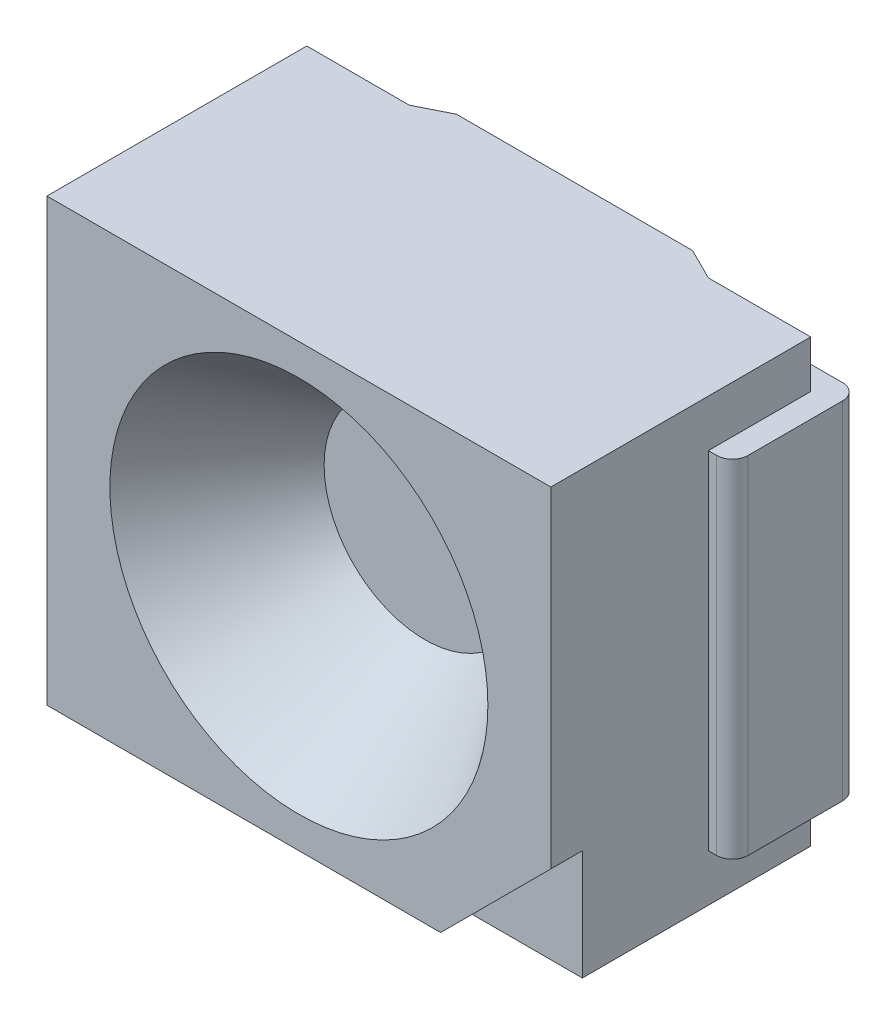
SolidWorks part; units mm, degrees
ref_plane "Front Plane" through (0, 0, 0) normal (0, 0, 1) x (1, 0, 0)
ref_plane "Top Plane" through (0, 0, 0) normal (0, 1, 0) x (1, 0, 0)
ref_plane "Right Plane" through (0, 0, 0) normal (1, 0, 0) x (0, 0, -1)
sketch "Sketch1" plane through (0, 0, 0) normal (0, 0, 1) x (1, 0, 0)
  line L1 (0, 0) -> (3.2, 0)
  line L2 (0, 0) -> (0, 2.8)
  line L3 (0, 2.8) -> (3.2, 2.8)
  line L4 (3.2, 0) -> (3.2, 2.8)
  dimension "D1" = 3.2
  dimension "D2" = 2.8
extrude "Boss-Extrude1" add sketch "Sketch1" along normal blind 1.75
sketch "Sketch2" plane through (0, 0, 1.75) normal (0, 0, 1) x (1, 0, 0)
  line L0 (3.2, 0) -> (3.2, 0.7)
  line L1 (3.2, 0) -> (3.2, 2.8) construction
  line L2 (3.2, 0.7) -> (2.5, 0)
  line L3 (0, 0) -> (3.2, 0) construction
  line L4 (2.5, 0) -> (3.2, 0)
  dimension "D1" = 0.7
  dimension "D2" = 0.7
extrude "Cut-Extrude1" cut sketch "Sketch2" against normal blind 0.2
sketch "Sketch3" plane through (0, 0, 1.75) normal (0, 0, 1) x (1, 0, 0)
  line L0 (3.2, 2.8) -> (0, 0) construction
  line L1 (0, 0) -> (0, 2.8) construction
  line L2 (0, 2.8) -> (3.2, 0) construction
  circle A0 centre (1.6, 1.4) radius 1.2
  dimension "D1" = 2.4
extrude "Cut-Extrude2" cut sketch "Sketch3" against normal blind 0.8 draft 35
sketch "Sketch5" plane through (0, 0, 0) normal (0, -1, 0) x (1, 0, 0)
  line L0 (1.6, 0) -> (1.6, 1.75) construction
  line L1 (0, 0) -> (3.2, 0) construction
  line L2 (0, 1.75) -> (2.5, 1.75) construction
  line L3 (0.85, 0) -> (2.35, 0) construction
  line L4 (0, 0.1) -> (0.65, 0.1)
  line L5 (0, 0.1) -> (0, 0)
  line L6 (0, 0) -> (0.65, 0)
  line L8 (2.55, 0.1) -> (3.2, 0.1)
  line L10 (2.55, 0) -> (3.2, 0)
  line L11 (3.2, 0.1) -> (3.2, 0)
  line L12 (0.65, 0.1) -> (0.85, 0)
  line L13 (0.85, 0) -> (0.65, 0)
  line L14 (2.55, 0.1) -> (2.35, 0)
  line L15 (2.35, 0) -> (2.55, 0)
  dimension "D1" = 0.1
  dimension "D2" = 0.65
  dimension "D3" = 1.5
  dimension "D4" = 0.1
  dimension "D5" = 0.65
extrude "Cut-Extrude3" cut sketch "Sketch5" against normal through all
sketch "Sketch6" plane through (0, 0, 0.1) normal (0, 0, -1) x (-1, 0, 0)
  line L0 (-2.875, 2.8) -> (-2.875, 0) construction
  line L1 (-3.2, 2.8) -> (-2.55, 2.8) construction
  line L2 (-3.2, 0) -> (-2.55, 0) construction
  line L3 (-2.875, 0) -> (-0.325, 0) construction
  line L4 (-0.65, 0) -> (0, 0) construction
  line L5 (-0.325, 0) -> (-0.325, 2.8) construction
  line L6 (-0.65, 2.8) -> (0, 2.8) construction
  line L7 (-3.2, 1.4) -> (0, 1.4) construction
  line L8 (-3.3525, 2.5) -> (-2.5525, 2.5)
  line L9 (-3.3525, 2.5) -> (-3.3525, 0.3)
  line L10 (-3.3525, 0.3) -> (-2.5525, 0.3)
  line L11 (-2.5525, 2.5) -> (-2.5525, 0.3)
  line L12 (-3.2, 2.8) -> (-3.2, 0) construction
  line L13 (0, 2.8) -> (0, 0) construction
  line L14 (0.15, 2.5) -> (0.15, 0.3)
  line L15 (-0.65, 2.5) -> (0.15, 2.5)
  line L16 (-0.65, 0.3) -> (0.15, 0.3)
  line L17 (-0.65, 2.5) -> (-0.65, 0.3)
  line L18 (-0.1725, 2.8) -> (-0.1725, 0) construction
  dimension "D1" = 0.8
  dimension "D2" = 2.2
  dimension "D3" = 0.8
  dimension "D4" = 2.2
extrude "Boss-Extrude3" add sketch "Sketch6" along normal blind 0.15
sketch "Sketch7" plane through (0, 0, 0.1) normal (0, 0, 1) x (1, 0, 0)
  line L0 (0, 0.3) -> (-0.15, 0.3) construction
  line L1 (-0.15, 2.5) -> (0, 2.5)
  line L2 (-0.15, 2.5) -> (-0.15, 0.3)
  line L3 (-0.15, 0.3) -> (0, 0.3)
  line L4 (0, 2.5) -> (0, 0.3)
  line L5 (0, 2.8) -> (0, 0) construction
  line L7 (3.3525, 0.3) -> (3.2, 0.3)
  line L8 (3.3525, 0.3) -> (3.3525, 2.5)
  line L9 (3.3525, 2.5) -> (3.2, 2.5)
  line L10 (3.2, 0.3) -> (3.2, 2.5)
extrude "Boss-Extrude4" add sketch "Sketch7" along normal blind 0.65
fillet "Fillet1" radius 0.1 4 edges at (3.3525, 1.4, -0.05) (3.3525, 1.4, 0.75) (-0.15, 1.4, -0.05) (-0.15, 1.4, 0.75)
sketch "Sketch8" plane through (0, 0, 0) normal (0, 0, -1) x (-1, 0, 0)
  circle A0 centre (-1.6, 1.4) radius 0.3
  dimension "D1" = 0.6
extrude "Cut-Extrude4" cut sketch "Sketch8" against normal blind 0.2
